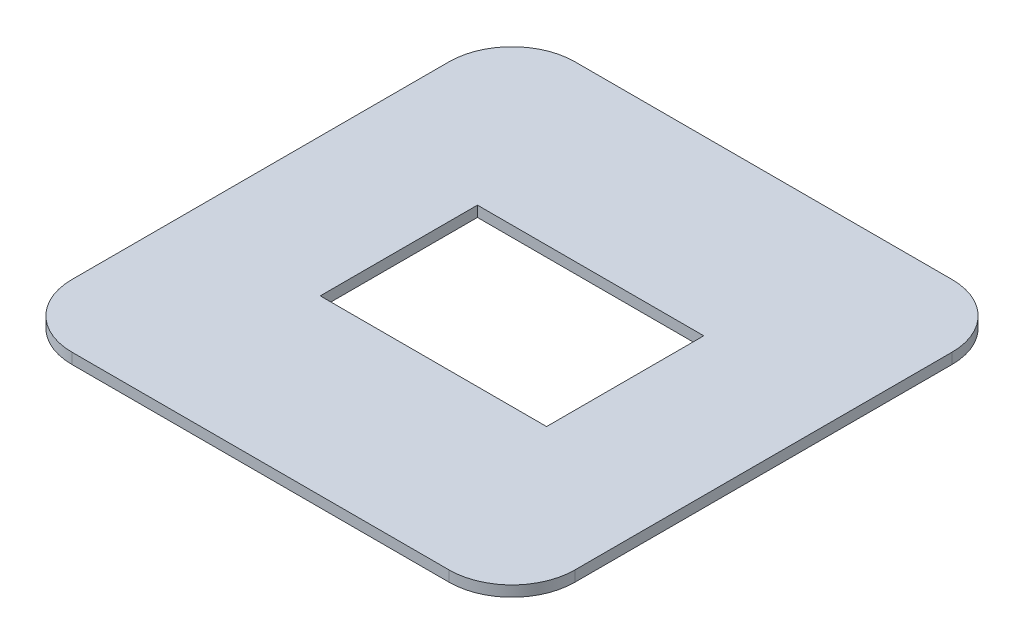
SolidWorks part; units mm, degrees
ref_plane "Plan de face" through (0, 0, 0) normal (0, 0, 1) x (1, 0, 0)
ref_plane "Plan de dessus" through (0, 0, 0) normal (0, 1, 0) x (1, 0, 0)
ref_plane "Plan de droite" through (0, 0, 0) normal (1, 0, 0) x (0, 0, -1)
sketch "Esquisse1" plane through (0, 0, 0) normal (0, 1, 0) x (1, 0, 0)
  line L1 (18, 12.5) -> (-18, 12.5)
  line L2 (18, 12.5) -> (18, -12.5)
  line L3 (18, -12.5) -> (-18, -12.5)
  line L4 (-18, 12.5) -> (-18, -12.5)
  line L5 (18, 12.5) -> (-18, -12.5) construction
  line L6 (18, -12.5) -> (-18, 12.5) construction
  line L7 (-40, -40) -> (40, -40)
  line L8 (-40, -40) -> (-40, 40)
  line L9 (-40, 40) -> (40, 40)
  line L10 (40, -40) -> (40, 40)
  line L11 (-40, -40) -> (40, 40) construction
  line L12 (-40, 40) -> (40, -40) construction
  point P0 (0, 0)
  point P5 (0, 0)
  dimension "D1" = 36
  dimension "D2" = 25
  dimension "D3" = 80
  dimension "D4" = 80
extrude "Boss.-Extru.1" add sketch "Esquisse1" along normal blind 1.7 contours L2 L1 L4 L3 | L8 L7 L10 L9
fillet "Congé1" radius 10 4 edges at (-40, 0.85, -40) (40, 0.85, -40) (40, 0.85, 40) (-40, 0.85, 40)
